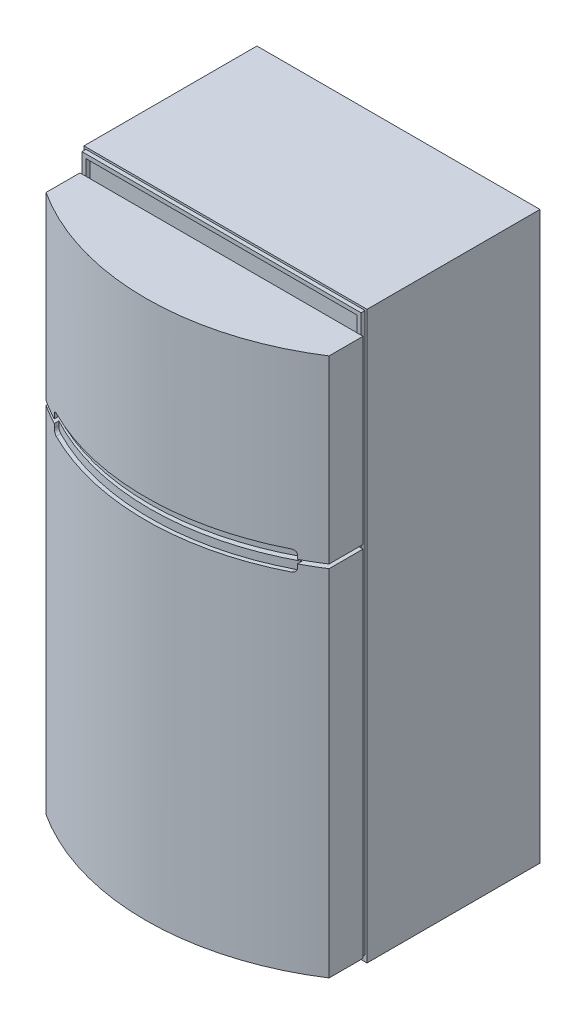
SolidWorks part; units mm, degrees
ref_plane "Front Plane" through (0, 0, 0) normal (0, 0, 1) x (1, 0, 0)
ref_plane "Top Plane" through (0, 0, 0) normal (0, 1, 0) x (1, 0, 0)
ref_plane "Right Plane" through (0, 0, 0) normal (1, 0, 0) x (0, 0, -1)
sketch "Sketch1" plane through (0, 0, 0) normal (0, 1, 0) x (1, 0, 0)
  line L1 (-450, -275) -> (450, -275)
  line L2 (-450, -275) -> (-450, 275)
  line L3 (-450, 275) -> (450, 275)
  line L4 (450, -275) -> (450, 275)
  line L5 (-450, -275) -> (450, 275) construction
  line L6 (-450, 275) -> (450, -275) construction
  point P0 (0, 0)
  dimension "D1" = 550
  dimension "D2" = 900
extrude "Boss-Extrude1" add sketch "Sketch1" along normal blind 1800
sketch "Sketch2" plane through (0, 0, 0) normal (0, 1, 0) x (1, 0, 0)
  line L0 (450, -275) -> (450, 275) construction
  line L1 (-450, -287.7) -> (450, -287.7)
  line L2 (-450, -287.7) -> (-450, -395.5833)
  line L3 (-450, -395.5833) -> (450, -395.5833) construction
  line L4 (450, -287.7) -> (450, -395.5833)
  line L5 (-450, 275) -> (-450, -275) construction
  line L6 (-450, -275) -> (450, -275) construction
  line L7 (0, -528.402) -> (0, -275) construction
  line L8 (450, 275) -> (-450, 275) construction
  arc A0 (-450, -395.5833) -> (450, -395.5833) centre (0, 300.3245) ccw
  dimension "D1" = 12.7
  dimension "D2" = 803.402
extrude "Boss-Extrude2" add sketch "Sketch2" along normal blind 1712.976 from offset 19.05 separate body
ref_plane "Plane1" through (0, 0, 528.402) normal (0, 0, 1) x (1, 0, 0)
sketch "Sketch3" plane through (0, 0, 528.402) normal (0, 0, 1) x (1, 0, 0)
  line L0 (-450, 1732.026) -> (-450, 19.05) construction
  line L1 (-450, 1158.8433) -> (450, 1158.8433)
  line L2 (-450, 1158.8433) -> (-450, 1146.1433)
  line L3 (-450, 1146.1433) -> (450, 1146.1433)
  line L4 (450, 1158.8433) -> (450, 1146.1433)
  line L5 (450, 1732.026) -> (450, 19.05) construction
  dimension "D1" = 12.7
extrude "Cut-Extrude1" cut sketch "Sketch3" against normal blind 1712.976
sketch "Sketch4" plane through (0, 0, 528.402) normal (0, 0, 1) x (1, 0, 0)
  line L0 (450, 1732.026) -> (450, 1158.8433) construction
  line L1 (-373.8, 1184.2433) -> (373.8, 1184.2433)
  line L2 (-386.5, 1171.5433) -> (-386.5, 1133.4433)
  line L3 (-373.8, 1120.7433) -> (373.8, 1120.7433)
  line L4 (386.5, 1171.5433) -> (386.5, 1133.4433)
  line L5 (0, 1184.2433) -> (0, 1158.8433) construction
  line L6 (-450, 1158.8433) -> (450, 1158.8433) construction
  line L7 (0, 1146.1433) -> (0, 1120.7433) construction
  line L8 (450, 1146.1433) -> (-450, 1146.1433) construction
  arc A0 (373.8, 1120.7433) -> (386.5, 1133.4433) centre (373.8, 1133.4433) ccw
  arc A1 (373.8, 1184.2433) -> (386.5, 1171.5433) centre (373.8, 1171.5433) cw
  arc A2 (-386.5, 1133.4433) -> (-373.8, 1120.7433) centre (-373.8, 1133.4433) ccw
  arc A3 (-373.8, 1184.2433) -> (-386.5, 1171.5433) centre (-373.8, 1171.5433) ccw
  point P16 (386.5, 1120.7433)
  point P19 (386.5, 1184.2433)
  dimension "D3" = 12.7
  dimension "D1" = 63.5
  dimension "D2" = 63.5
extrude "Cut-Extrude2" cut sketch "Sketch4" against normal offset from surface (103.3488 mm away) 12.7
sketch "Sketch5" plane through (0, 0, 275) normal (0, 0, 1) x (1, 0, 0)
  line L0 (-450, 0) -> (450, 0) construction
  line L1 (450, 1146.1433) -> (450, 19.05) construction
  line L2 (-450, 1146.1433) -> (-450, 19.05) construction
  line L5 (-450, 1800) -> (450, 1800) construction
  line L12 (-443.65, 19.05) -> (443.65, 19.05)
  line L13 (443.65, 19.05) -> (443.65, 1793.65)
  line L14 (443.65, 1793.65) -> (-443.65, 1793.65)
  line L15 (-443.65, 1793.65) -> (-443.65, 19.05)
  dimension "D1" = 19.05
  dimension "D2" = 6.35
  dimension "D3" = 6.35
  dimension "D4" = 6.35
extrude "Extrude-Thin1" add sketch "Sketch5" along normal blind 12.7 separate body thin thin type one direction reverse wall 12.7
sketch "Sketch6" plane through (0, 0, 275) normal (0, 0, 1) x (1, 0, 0)
  line L0 (-302.626, 0) -> (-268.0274, 13.4836)
  line L1 (-450, 0) -> (450, 0) construction
  line L2 (-268.0274, 13.4836) -> (268.0274, 13.4836)
  line L3 (0, 13.4836) -> (0, 0) construction
  line L4 (302.626, 0) -> (-302.626, 0)
  line L5 (302.626, 0) -> (268.0274, 13.4836)
extrude "Cut-Extrude3" cut sketch "Sketch6" against normal through all
